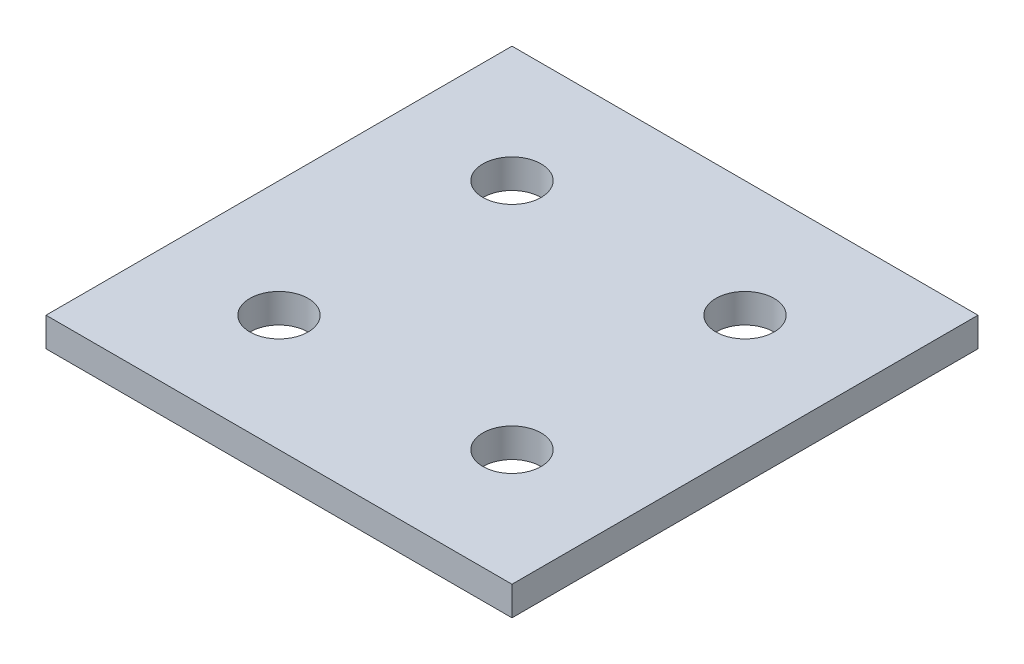
SolidWorks part; units mm, degrees
material "Plain Carbon Steel"
ref_plane "Front Plane" through (0, 0, 0) normal (0, 0, 1) x (1, 0, 0)
ref_plane "Top Plane" through (0, 0, 0) normal (0, 1, 0) x (1, 0, 0)
ref_plane "Right Plane" through (0, 0, 0) normal (1, 0, 0) x (0, 0, -1)
sketch "Sketch1" plane through (0, 0, 0) normal (0, 1, 0) x (1, 0, 0)
  line L1 (0, 0) -> (101.6, 0)
  line L2 (0, 0) -> (0, 101.6)
  line L3 (0, 101.6) -> (101.6, 101.6)
  line L4 (101.6, 0) -> (101.6, 101.6)
  dimension "D1" = 101.6
  dimension "D2" = 101.6
extrude "Boss-Extrude1" add sketch "Sketch1" along normal blind 6.35
hole_wizard "1/2 (0.5000) Dowel Hole1" positions "3DSketch1" profile "Sketch2" hole size "1/2" standard "ANSI Inch" end condition through all
sketch3d "3DSketch1"
  line L0 (0, 6.35, -101.6) -> (0, 6.35, 0) construction
  line L1 (101.6, 6.35, -101.6) -> (0, 6.35, -101.6) construction
  line L2 (0, 6.35, 0) -> (101.6, 6.35, 0) construction
  line L3 (101.6, 6.35, 0) -> (101.6, 6.35, -101.6) construction
  point P0 (25.4, 6.35, -25.4)
  point P2 (25.4, 6.35, -76.2)
  point P4 (76.2, 6.35, -76.2)
  point P6 (76.2, 6.35, -25.4)
  dimension "D1" = 25.4
  dimension "D2" = 76.2
  dimension "D3" = 25.4
  dimension "D4" = 25.4
  dimension "D5" = 25.4
  dimension "D6" = 25.4
  dimension "D7" = 25.4
  dimension "D8" = 25.4
sketch "Sketch2" plane through (25.4, 6.35, -25.4) normal (1, 0, 0) x (0, 0, 1)
  line L0 (0, 0) -> (0, 6.35)
  line L1 (0, 6.35) -> (6.35, 6.35)
  line L2 (6.35, 6.35) -> (6.35, 0)
  line L5 (6.35, 0) -> (0, 0)
  line L11 (0, -6.35) -> (0, 107.95) construction
  dimension "Thru Hole Dia." = 12.7
  dimension "Thru Hole Depth" = 6.35
